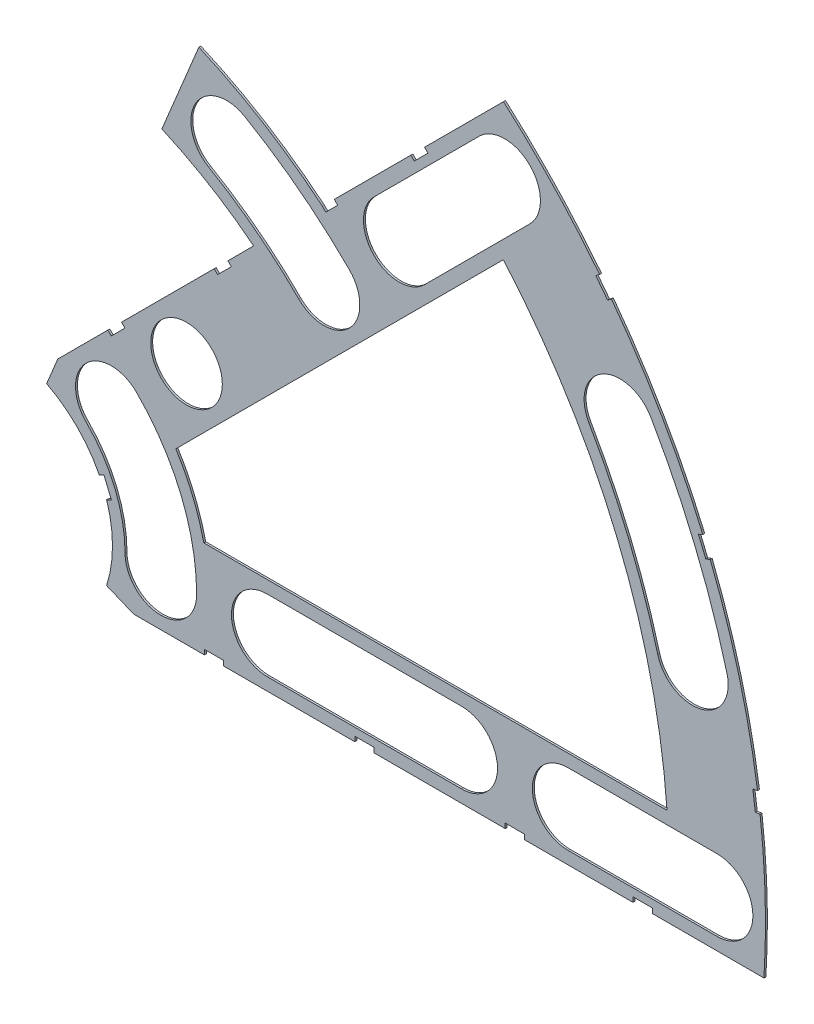
SolidWorks part; units mm, degrees
material "PTFE (general)"
ref_plane "Front Plane" through (0, 0, 0) normal (0, 0, 1) x (1, 0, 0)
ref_plane "Top Plane" through (0, 0, 0) normal (0, 1, 0) x (1, 0, 0)
ref_plane "Right Plane" through (0, 0, 0) normal (1, 0, 0) x (0, 0, -1)
sketch "Sketch1" plane through (0, 0, 0) normal (0, 0, 1) x (1, 0, 0)
  line L0 (0, 0) -> (320.3893, 0) construction
  line L1 (0, 0) -> (155.5285, 155.5285) construction
  line L2 (27.2188, 62.3934) -> (22.3577, 50.6576)
  line L3 (8.6967, 17.6769) -> (7.229, 14.1336)
  line L4 (101.4014, -6.35) -> (18.6489, -6.35)
  line L5 (15.1056, -4.8823) -> (18.6489, -6.35)
  line L6 (88.6729, 6.35) -> (27.8605, 6.35)
  line L7 (67.2115, 76.1917) -> (43.4342, 52.4144)
  line L8 (34.4055, 43.3857) -> (8.6967, 17.6769)
  line L9 (67.1914, 58.2111) -> (24.1905, 15.2102)
  line L10 (0, 0) -> (40.4486, 97.6516) construction
  line L11 (0, 0) -> (123.4567, -51.1374) construction
  line L18 (8.6967, 17.6769) -> (13.294, 8.6183) construction
  line L19 (18.6489, -6.35) -> (15.4943, 3.3063) construction
  line L20 (27.8605, 6.35) -> (27.7442, 6.7059) construction
  line L21 (24.1905, 15.2102) -> (24.3599, 14.8764) construction
  line L22 (67.2115, 76.1917) -> (8.6967, 17.6769) construction
  arc A0 (7.229, 14.1336) -> (15.1056, -4.8823) centre (0, 0) cw
  arc A1 (67.2115, 76.1917) -> (101.4014, -6.35) centre (0, 0) cw
  arc A2 (24.1905, 15.2102) -> (27.8605, 6.35) centre (0, 0) cw
  arc A3 (67.1914, 58.2111) -> (88.6729, 6.35) centre (0, 0) cw
  arc A4 (27.2188, 62.3934) -> (43.4342, 52.4144) centre (0, 0) cw
  arc A5 (22.3577, 50.6576) -> (34.4055, 43.3857) centre (0, 0) cw
  arc A8 (13.294, 8.6183) -> (15.4943, 3.3063) centre (0, 0) cw construction
  arc A9 (24.3599, 14.8764) -> (27.7442, 6.7059) centre (0, 0) cw construction
  dimension "D1" = 45
  dimension "D3" = 6.35
  dimension "D4" = 15.875
  dimension "D7" = 22.5
  dimension "D8" = 101.6
  dimension "D11" = 12.7
  dimension "D12" = 12.7
  dimension "D2" = 55.372
  dimension "D13" = 12.7
  dimension "D5" = 67.5
  dimension "D9" = 1.27
  dimension "D10" = 1.27
  dimension "D14" = 6.35
  dimension "D15" = 6.35
  dimension "D16" = 1.27
  dimension "D6" = 12.7
extrude "Boss-Extrude1" add sketch "Sketch1" along normal blind 0.254
sketch "Sketch2" plane through (0, 0, 0.254) normal (0, 0, 1) x (1, 0, 0)
  line L0 (0, 0) -> (101.6, 0) construction
  line L1 (0, 0) -> (71.842, 71.842) construction
  line L2 (0, 0) -> (30.861, 53.4528) construction
  line L3 (0, 0) -> (22.225, 0) construction
  line L4 (0, 0) -> (15.7154, 15.7154) construction
  line L5 (0, 0) -> (95.25, 0) construction
  line L6 (0, 0) -> (92.0044, 24.6525) construction
  arc A0 (101.4014, -6.35) -> (67.2115, 76.1917) centre (0, 0) ccw construction
  circle A1 centre (22.225, 0) radius 4.699
  arc A2 (15.1056, -4.8823) -> (7.229, 14.1336) centre (0, 0) ccw construction
  circle A3 centre (36.195, 0) radius 4.699
  circle A4 centre (61.722, 0) radius 4.699
  circle A5 centre (75.692, 0) radius 4.699
  circle A6 centre (95.25, 0) radius 4.699
  circle A7 centre (15.7154, 15.7154) radius 4.699
  circle A8 centre (25.5937, 25.5937) radius 4.699
  circle A9 centre (43.644, 43.644) radius 4.699
  circle A10 centre (53.5223, 53.5223) radius 4.699
  circle A11 centre (92.0044, 24.6525) radius 4.699
  circle A12 centre (82.4889, 47.625) radius 4.699
  circle A13 centre (67.3519, 67.3519) radius 4.699
  circle A14 centre (30.861, 53.4528) radius 4.699
  arc A15 (43.4342, 52.4144) -> (27.2188, 62.3934) centre (0, 0) ccw construction
  dimension "D3" = 9.398
  dimension "D1" = 45
  dimension "D2" = 6.35
  dimension "D4" = 6.35
  dimension "D5" = 13.97
  dimension "D7" = 13.97
  dimension "D8" = 19.558
  dimension "D9" = 45
  dimension "D10" = 15
  dimension "D11" = 15
  dimension "D12" = 6.35
  dimension "D6" = 25.527
  dimension "D13" = 2
extrude "Cut-Extrude1" cut sketch "Sketch2" against normal through all
sketch "Sketch3" plane through (0, 0, 0.254) normal (0, 0, 1) x (1, 0, 0)
  line L0 (15.2664, 24.2467) -> (17.0625, 26.0427)
  line L1 (15.2664, 24.2467) -> (15.7154, 23.7977)
  line L2 (17.0625, 26.0427) -> (17.5115, 25.5937)
  line L3 (15.7154, 23.7977) -> (17.5115, 25.5937)
  line L5 (43.4342, 52.4144) -> (44.9911, 53.9713)
  line L6 (43.4342, 52.4144) -> (43.8832, 51.9654)
  line L7 (44.9911, 53.9713) -> (45.4401, 53.5223)
  line L8 (43.8832, 51.9654) -> (45.4401, 53.5223)
  line L9 (27.94, -6.35) -> (30.48, -6.35)
  line L10 (27.94, -6.35) -> (27.94, -5.715)
  line L11 (30.48, -6.35) -> (30.48, -5.715)
  line L12 (27.94, -5.715) -> (30.48, -5.715)
  line L13 (18.6489, -6.35) -> (101.4014, -6.35) construction
  line L14 (67.437, -6.35) -> (69.977, -6.35)
  line L15 (67.437, -6.35) -> (67.437, -5.715)
  line L16 (69.977, -6.35) -> (69.977, -5.715)
  line L17 (67.437, -5.715) -> (69.977, -5.715)
  line L18 (29.2307, 38.211) -> (31.0268, 40.007)
  line L19 (29.2307, 38.211) -> (29.6797, 37.762)
  line L20 (31.0268, 40.007) -> (31.4758, 39.558)
  line L21 (29.6797, 37.762) -> (31.4758, 39.558)
  line L22 (56.845, 65.8253) -> (55.049, 64.0292)
  line L23 (56.845, 65.8253) -> (57.294, 65.3763)
  line L24 (55.049, 64.0292) -> (55.498, 63.5802)
  line L25 (57.294, 65.3763) -> (55.498, 63.5802)
  line L26 (47.6885, -6.35) -> (50.2285, -6.35)
  line L27 (47.6885, -6.35) -> (47.6885, -5.715)
  line L28 (50.2285, -6.35) -> (50.2285, -5.715)
  line L29 (47.6885, -5.715) -> (50.2285, -5.715)
  line L30 (84.201, -6.35) -> (86.741, -6.35)
  line L31 (84.201, -6.35) -> (84.201, -5.715)
  line L32 (86.741, -6.35) -> (86.741, -5.715)
  line L33 (84.201, -5.715) -> (86.741, -5.715)
  line L34 (0, 0) -> (100.7308, 13.2615) construction
  line L35 (0, 0) -> (93.8662, 38.8806) construction
  line L36 (0, 0) -> (80.6047, 61.8502) construction
  line L37 (0, 0) -> (101.6, 0) construction
  line L38 (99.9355, 14.4377) -> (100.267, 11.9194)
  line L39 (99.9355, 14.4377) -> (101.1946, 14.6035)
  line L40 (100.267, 11.9194) -> (101.5261, 12.0852)
  line L41 (101.1946, 14.6035) -> (101.5261, 12.0852)
  line L42 (99.9355, 14.4377) -> (101.5261, 12.0852) construction
  line L43 (100.267, 11.9194) -> (101.1946, 14.6035) construction
  line L44 (93.7655, 37.4643) -> (94.9388, 37.9503)
  line L45 (93.7655, 37.4643) -> (92.7935, 39.811)
  line L46 (94.9388, 37.9503) -> (93.9668, 40.297)
  line L47 (92.7935, 39.811) -> (93.9668, 40.297)
  line L48 (93.7655, 37.4643) -> (93.9668, 40.297) construction
  line L49 (94.9388, 37.9503) -> (92.7935, 39.811) construction
  line L50 (79.3278, 62.4712) -> (80.874, 60.456)
  line L51 (79.3278, 62.4712) -> (80.3354, 63.2443)
  line L52 (80.874, 60.456) -> (81.8816, 61.2292)
  line L53 (80.3354, 63.2443) -> (81.8816, 61.2292)
  line L54 (79.3278, 62.4712) -> (81.8816, 61.2292) construction
  line L55 (80.874, 60.456) -> (80.3354, 63.2443) construction
  line L56 (13.5939, 7.0054) -> (14.5659, 4.6588)
  line L57 (13.5939, 7.0054) -> (14.7672, 7.4914)
  line L58 (14.5659, 4.6588) -> (15.7393, 5.1448)
  line L59 (14.7672, 7.4914) -> (15.7393, 5.1448)
  line L60 (13.5939, 7.0054) -> (15.7393, 5.1448) construction
  line L61 (14.5659, 4.6588) -> (14.7672, 7.4914) construction
  line L62 (34.4055, 43.3857) -> (8.6967, 17.6769) construction
  line L63 (67.2115, 76.1917) -> (43.4342, 52.4144) construction
  circle A0 centre (15.7154, 15.7154) radius 4.699 construction
  circle A1 centre (53.5223, 53.5223) radius 4.699 construction
  circle A2 centre (22.225, 0) radius 4.699 construction
  circle A3 centre (61.722, 0) radius 4.699 construction
  arc A4 (101.4014, -6.35) -> (67.2115, 76.1917) centre (0, 0) ccw construction
  arc A9 (15.1056, -4.8823) -> (7.229, 14.1336) centre (0, 0) ccw construction
  circle A10 centre (36.195, 0) radius 4.699 construction
  circle A11 centre (75.692, 0) radius 4.699 construction
  circle A12 centre (25.5937, 25.5937) radius 4.699 construction
  circle A13 centre (53.5223, 53.5223) radius 4.699 construction
  point P75 (14.6666, 6.0751)
  dimension "D2" = 5.715
  dimension "D3" = 2.54
  dimension "D8" = 0.635
  dimension "D9" = 5.715
  dimension "D12" = 5.715
  dimension "D4" = 7.5
  dimension "D5" = 22.5
  dimension "D7" = 37.5
  dimension "D10" = 90
  dimension "D11" = 1.27
  dimension "D14" = 0.635
  dimension "D15" = 90
  dimension "D18" = 0.635
  dimension "D19" = 90
  dimension "D22" = 0.635
  dimension "D20" = 1.27
  dimension "D17" = 0.635
  dimension "D21" = 5.715
  dimension "D13" = 11.4935
  dimension "D16" = 8.509
  dimension "D23" = 11.4935
  dimension "D24" = 8.509
  dimension "D25" = 2.54
extrude "Cut-Extrude2" cut sketch "Sketch3" against normal through all
sketch "Sketch7" plane through (0, 0, 0.254) normal (0, 0, 1) x (1, 0, 0)
  line L0 (36.195, 0) -> (61.722, 0) construction
  line L1 (36.195, 4.699) -> (61.722, 4.699)
  line L2 (36.195, -4.699) -> (61.722, -4.699)
  line L3 (75.692, 0) -> (95.25, 0) construction
  line L4 (75.692, 4.699) -> (95.25, 4.699)
  line L5 (75.692, -4.699) -> (95.25, -4.699)
  line L6 (53.5223, 53.5223) -> (67.3519, 67.3519) construction
  line L7 (50.1996, 56.845) -> (64.0292, 70.6746)
  line L8 (56.845, 50.1996) -> (70.6746, 64.0292)
  arc A0 (43.644, 43.644) -> (30.861, 53.4528) centre (0, 0) ccw construction
  arc A1 (46.9667, 46.9667) -> (33.2105, 57.5223) centre (0, 0) ccw
  arc A2 (40.3213, 40.3213) -> (28.5115, 49.3834) centre (0, 0) ccw
  arc A3 (40.3213, 40.3213) -> (46.9667, 46.9667) centre (43.644, 43.644) ccw
  arc A4 (33.2105, 57.5223) -> (28.5115, 49.3834) centre (30.861, 53.4528) ccw
  circle A5 centre (30.861, 53.4528) radius 4.699 construction
  circle A6 centre (43.644, 43.644) radius 4.699 construction
  arc A7 (22.225, 0) -> (15.7154, 15.7154) centre (0, 0) ccw construction
  arc A8 (26.924, 0) -> (19.0381, 19.0381) centre (0, 0) ccw
  arc A9 (17.526, 0) -> (12.3928, 12.3928) centre (0, 0) ccw
  arc A10 (17.526, 0) -> (26.924, 0) centre (22.225, 0) ccw
  arc A11 (19.0381, 19.0381) -> (12.3928, 12.3928) centre (15.7154, 15.7154) ccw
  arc A12 (92.0044, 24.6525) -> (82.4889, 47.625) centre (0, 0) ccw construction
  arc A13 (96.5433, 25.8687) -> (86.5584, 49.9745) centre (0, 0) ccw
  arc A14 (87.4655, 23.4363) -> (78.4195, 45.2755) centre (0, 0) ccw
  arc A15 (87.4655, 23.4363) -> (96.5433, 25.8687) centre (92.0044, 24.6525) ccw
  arc A16 (86.5584, 49.9745) -> (78.4195, 45.2755) centre (82.4889, 47.625) ccw
  arc A17 (36.195, 4.699) -> (36.195, -4.699) centre (36.195, 0) ccw
  arc A18 (61.722, -4.699) -> (61.722, 4.699) centre (61.722, 0) ccw
  arc A19 (75.692, 4.699) -> (75.692, -4.699) centre (75.692, 0) ccw
  arc A20 (95.25, -4.699) -> (95.25, 4.699) centre (95.25, 0) ccw
  arc A21 (50.1996, 56.845) -> (56.845, 50.1996) centre (53.5223, 53.5223) ccw
  arc A22 (70.6746, 64.0292) -> (64.0292, 70.6746) centre (67.3519, 67.3519) ccw
  circle A33 centre (15.7154, 15.7154) radius 4.699 construction
  circle A34 centre (22.225, 0) radius 4.699 construction
  circle A35 centre (36.195, 0) radius 4.699 construction
  circle A36 centre (61.722, 0) radius 4.699 construction
  circle A37 centre (75.692, 0) radius 4.699 construction
  circle A38 centre (95.25, 0) radius 4.699 construction
  circle A39 centre (92.0044, 24.6525) radius 4.699 construction
  circle A40 centre (82.4889, 47.625) radius 4.699 construction
  circle A41 centre (67.3519, 67.3519) radius 4.699 construction
  circle A42 centre (53.5223, 53.5223) radius 4.699 construction
  point P5 (37.574, 48.9674)
  point P19 (20.5332, 8.5051)
  point P24 (87.9995, 36.4506)
  point P38 (48.9585, 0)
  point P43 (85.471, 0)
  point P52 (60.4371, 60.4371)
  dimension "D1" = 9.398
  dimension "D2" = 9.398
  dimension "D3" = 9.398
  dimension "D5" = 9.398
  dimension "D4" = 9.398
  dimension "D6" = 9.398
extrude "Cut-Extrude3" cut sketch "Sketch7" against normal through all
equation "\"LayerThick\"=0.01"
equation "\"D1@Boss-Extrude1\"=\"LayerThick\""
equation "\"CoilSep\"= 1.005"
equation "\"D6@Sketch2\"=\"CoilSep\""
equation "\"CoilSep2\"= \"D8@Sketch2\""
equation "\"D13@Sketch3\"=\"CoilSep\"/2-.05"
equation "\"D16@Sketch3\"=\"CoilSep2\"/2-.05"
equation "\"D23@Sketch3\"=\"CoilSep\"/2-.05"
equation "\"D24@Sketch3\"=\"CoilSep2\"/2-.05"
